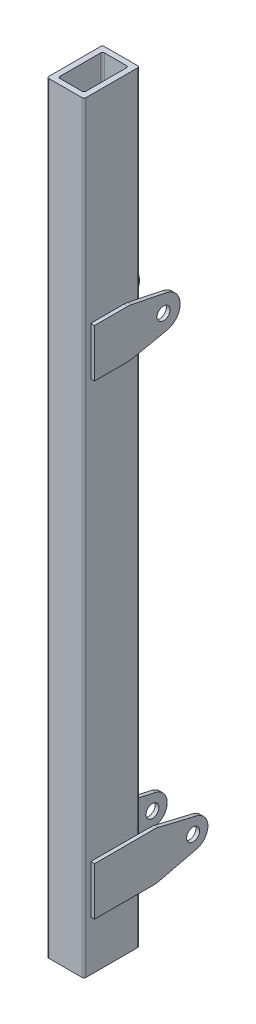
SolidWorks part; units mm, degrees
ref_plane "Front Plane" through (0, 0, 0) normal (0, 0, 1) x (1, 0, 0)
ref_plane "Top Plane" through (0, 0, 0) normal (0, 1, 0) x (1, 0, 0)
ref_plane "Right Plane" through (0, 0, 0) normal (1, 0, 0) x (0, 0, -1)
sketch "Sketch1" plane through (0, 0, 0) normal (0, 1, 0) x (1, 0, 0)
  line L1 (-45, -75) -> (45, -75)
  line L2 (-50, -70) -> (-50, 70)
  line L3 (-45, 75) -> (45, 75)
  line L4 (50, -70) -> (50, 70)
  line L5 (-50, -75) -> (50, 75) construction
  line L6 (-50, 75) -> (50, -75) construction
  line L7 (-30, -60) -> (30, -60)
  line L8 (-35, -55) -> (-35, 55)
  line L9 (-30, 60) -> (30, 60)
  line L10 (35, -55) -> (35, 55)
  line L11 (-35, -60) -> (35, 60) construction
  line L12 (-35, 60) -> (35, -60) construction
  arc A0 (-35, -55) -> (-30, -60) centre (-30, -55) ccw
  arc A1 (35, -55) -> (30, -60) centre (30, -55) cw
  arc A2 (50, -70) -> (45, -75) centre (45, -70) cw
  arc A3 (-45, -75) -> (-50, -70) centre (-45, -70) cw
  arc A4 (35, 55) -> (30, 60) centre (30, 55) ccw
  arc A5 (50, 70) -> (45, 75) centre (45, 70) ccw
  arc A6 (-30, 60) -> (-35, 55) centre (-30, 55) ccw
  arc A7 (-45, 75) -> (-50, 70) centre (-45, 70) ccw
  point P0 (0, 0)
  point P6 (0, 0)
  dimension "D5" = 5
  dimension "D1" = 100
  dimension "D2" = 150
  dimension "D3" = 15
  dimension "D4" = 15
extrude "Boss-Extrude1" add sketch "Sketch1" along normal blind 2060
sketch "Sketch2" plane through (50, 0, 0) normal (1, 0, 0) x (0, 0, -1)
  line L0 (-198.7363, 200) -> (210, 200) construction
  line L1 (43.3954, 1396.0454) -> (139.154, 1415.9409)
  line L2 (-198.7363, 1460) -> (195.8092, 1460) construction
  line L3 (-70, 0) -> (70, 0) construction
  line L4 (139.154, 1504.0591) -> (43.3954, 1523.9546)
  line L5 (-70, 2060) -> (70, 2060) construction
  line L6 (75, 2060) -> (75, 0) construction
  line L7 (-56.6365, 1460) -> (-56.6365, 1395)
  line L8 (-56.6365, 1460) -> (-56.6365, 1525)
  line L9 (-56.6365, 1395) -> (33.2242, 1395)
  line L10 (-56.6365, 1525) -> (33.2242, 1525)
  line L11 (-75, 2060) -> (-75, 0) construction
  line L12 (-56.6365, 200) -> (-56.6365, 265)
  line L13 (-56.6365, 200) -> (-56.6365, 135)
  line L14 (-56.6365, 135) -> (104.4326, 135)
  line L15 (-56.6365, 265) -> (104.4326, 265)
  line L16 (116.078, 136.3751) -> (219.3163, 161.1)
  line L17 (116.078, 263.6249) -> (219.3163, 238.9)
  circle A0 centre (130, 1460) radius 17.5
  arc A2 (139.154, 1415.9409) -> (139.154, 1504.0591) centre (130, 1460) ccw
  circle A3 centre (210, 200) radius 17.5
  arc A4 (219.3163, 161.1) -> (219.3163, 238.9) centre (210, 200) ccw
  arc A5 (116.078, 136.3751) -> (104.4326, 135) centre (104.4326, 185) cw
  arc A6 (116.078, 263.6249) -> (104.4326, 265) centre (104.4326, 215) ccw
  arc A7 (43.3954, 1523.9546) -> (33.2242, 1525) centre (33.2242, 1475) ccw
  arc A8 (43.3954, 1396.0454) -> (33.2242, 1395) centre (33.2242, 1445) cw
  point P37 (38.3635, 1525)
  point P40 (38.3635, 1395)
  dimension "D3" = 35
  dimension "D5" = 18.3635
  dimension "D11" = 45
  dimension "D13" = 35
  dimension "D15" = 50
  dimension "D16" = 40
  dimension "D1" = 200
  dimension "D2" = 600
  dimension "D4" = 55
  dimension "D6" = 65
  dimension "D7" = 65
  dimension "D8" = 65
  dimension "D9" = 95
  dimension "D10" = 95
  dimension "D12" = 65
  dimension "D14" = 135
extrude "Boss-Extrude2" add sketch "Sketch2" along normal blind 10
sketch "Sketch4" plane through (-50, 0, 0) normal (-1, 0, 0) x (0, 0, 1)
  line L0 (-210, 200) -> (157.7614, 200) construction
  line L1 (-219.3163, 238.9) -> (-109.9014, 263.7575)
  line L2 (-109.9014, 136.2425) -> (-219.3163, 161.1)
  line L3 (-130, 1460) -> (157.7226, 1460) construction
  line L4 (56.64, 1460) -> (56.64, 1525)
  line L5 (56.64, 1460) -> (56.64, 1395)
  line L6 (75, 2060) -> (75, 0) construction
  line L7 (56.64, 1525) -> (-33.2209, 1525)
  line L8 (56.64, 1395) -> (-33.2209, 1395)
  line L9 (-43.3917, 1396.0454) -> (-139.154, 1415.9409)
  line L10 (-43.3917, 1523.9546) -> (-139.154, 1504.0591)
  line L11 (56.64, 200) -> (56.64, 265)
  line L12 (56.64, 200) -> (56.64, 135)
  line L13 (56.64, 265) -> (-98.8244, 265)
  line L14 (56.64, 135) -> (-98.8244, 135)
  circle A0 centre (-210, 200) radius 17.5
  arc A1 (-219.3163, 238.9) -> (-219.3163, 161.1) centre (-210, 200) ccw
  circle A2 centre (-130, 1460) radius 17.5
  arc A3 (-139.154, 1504.0591) -> (-139.154, 1415.9409) centre (-130, 1460) ccw
  arc A4 (-33.2209, 1395) -> (-43.3917, 1396.0454) centre (-33.2209, 1445) cw
  arc A5 (-43.3917, 1523.9546) -> (-33.2209, 1525) centre (-33.2209, 1475) cw
  arc A6 (-98.8244, 135) -> (-109.9014, 136.2425) centre (-98.8244, 185) cw
  arc A7 (-98.8244, 265) -> (-109.9014, 263.7575) centre (-98.8244, 215) ccw
  point P31 (-38.36, 1395)
  point P34 (-38.36, 1525)
  point P40 (-104.4326, 135)
  point P43 (-104.4326, 265)
  dimension "D6" = 50
  dimension "D9" = 50
  dimension "D1" = 65
  dimension "D2" = 65
  dimension "D3" = 18.36
  dimension "D4" = 95
  dimension "D5" = 95
  dimension "D7" = 65
  dimension "D8" = 65
extrude "Boss-Extrude3" add sketch "Sketch4" along normal blind 10
